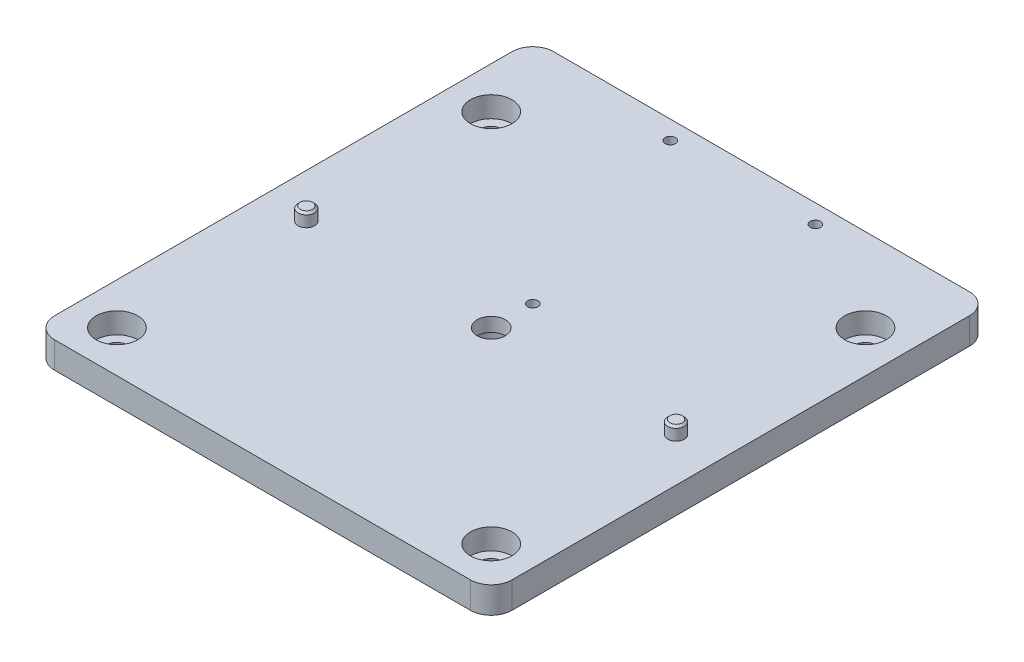
SolidWorks part; units mm, degrees
material "6061 Alloy"
ref_plane "Front Plane" through (0, 0, 0) normal (0, 0, 1) x (1, 0, 0)
ref_plane "Top Plane" through (0, 0, 0) normal (0, 1, 0) x (1, 0, 0)
ref_plane "Right Plane" through (0, 0, 0) normal (1, 0, 0) x (0, 0, -1)
sketch "Sketch1" plane through (0, 0, 0) normal (0, 1, 0) x (1, 0, 0)
  line L1 (-50, -55) -> (50, -55)
  line L2 (-55, -50) -> (-55, 55)
  line L3 (-55, 55) -> (55, 55)
  line L4 (55, -50) -> (55, 55)
  line L5 (-55, -55) -> (55, 55) construction
  line L6 (-55, 55) -> (55, -55) construction
  arc A0 (-55, -50) -> (-50, -55) centre (-50, -50) ccw
  arc A1 (50, -55) -> (55, -50) centre (50, -50) ccw
  point P0 (0, 0)
  dimension "D3" = 5
  dimension "D1" = 110
  dimension "D2" = 110
extrude "Boss-Extrude1" add sketch "Sketch1" along normal blind 6.35
sketch "Sketch9" plane through (0, 0, 0) normal (0, 1, 0) x (1, 0, 0)
  line L0 (55, 55) -> (20, 65)
  line L1 (55, 55) -> (-55, 55) construction
  line L2 (20, 65) -> (-20, 65)
  line L3 (-20, 65) -> (-55, 55)
  line L4 (55, 55) -> (-55, 55) construction
  line L5 (55, 55) -> (-55, 55)
  point P11 (0, 65)
  dimension "D1" = 10
  dimension "D2" = 40
hole_wizard "CBORE for 1/4 Socket Head Cap Screw1" positions "Sketch2" profile "Sketch4" counterbore size "1/4" standard "ANSI Inch" end condition through all
sketch "Sketch2" plane through (0, 0, 0) normal (0, -1, 0) x (-1, 0, 0)
  point P0 (0, 0)
sketch "Sketch4" plane through (0, 0, 0) normal (1, 0, 0) x (0, 0, -1)
  line L0 (0, 0) -> (0, 6.35)
  line L1 (0, 6.35) -> (3.3782, 6.35)
  line L3 (3.3782, 6.35) -> (3.3782, 3)
  line L4 (3.3782, 3) -> (5.5562, 3)
  line L5 (5.5562, 3) -> (5.5562, 0)
  line L7 (5.5562, 0) -> (0, 0)
  line L11 (0, -6.35) -> (0, 107.95) construction
  dimension "Thru Hole Dia." = 6.7564
  dimension "Thru Hole Depth" = 6.35
  dimension "C'Bore Dia." = 11.1125
  dimension "C'Bore Depth" = 3
hole_wizard "CBORE for M5 SHCS1" positions "Sketch5" profile "Sketch6" counterbore size "M5" standard "ANSI Metric"
sketch "Sketch5" plane through (0, 6.35, 0) normal (0, 1, 0) x (1, 0, 0)
  line L1 (55, 55) -> (-55, 55) construction
  line L2 (0, 0) -> (52.5, 0) construction
  line L4 (0, 0) -> (0, 55) construction
  point P0 (45, 45)
  point P16 (45, -45)
  point P17 (-45, -45)
  point P18 (-45, 45)
  dimension "D1" = 45
  dimension "D2" = 45
sketch "Sketch6" plane through (45, 6.35, -45) normal (1, 0, 0) x (0, 0, 1)
  line L0 (0, 0) -> (0, 13.2424)
  line L1 (0, 13.2424) -> (2.75, 11.59)
  line L2 (2.75, 11.59) -> (2.75, 5)
  line L3 (2.75, 5) -> (5, 5)
  line L4 (5, 5) -> (5, 0)
  line L5 (5, 0) -> (0, 0)
  line L10 (0, 13.2424) -> (-2.75, 11.59) construction
  line L11 (0, -6.35) -> (0, 107.95) construction
  dimension "Hole Dia." = 5.5
  dimension "Hole Depth" = 11.59
  dimension "C'Bore Dia." = 10
  dimension "C'Bore Depth" = 5
  dimension "Drill Angle" = 118
hole_wizard "1/8 (0.125) Press Dowel Hole1" positions "Sketch7" profile "Sketch8" hole size "1/8" standard "ANSI Inch" end condition through all
sketch "Sketch7" plane through (0, 6.35, 0) normal (0, 1, 0) x (1, 0, 0)
  line L0 (0, 0) -> (0, -55) construction
  line L1 (-50, -55) -> (50, -55) construction
  point P0 (-44.45, 0)
  point P2 (44.45, 0)
  dimension "D1" = 88.9
sketch "Sketch8" plane through (-44.45, 6.35, 0) normal (1, 0, 0) x (0, 0, 1)
  line L0 (0, 0) -> (0, 6.35)
  line L1 (0, 6.35) -> (1.9844, 6.35)
  line L2 (1.9844, 6.35) -> (1.9844, 0)
  line L5 (1.9844, 0) -> (0, 0)
  line L11 (0, -6.35) -> (0, 107.95) construction
  dimension "Thru Hole Dia." = 3.9688
  dimension "Thru Hole Depth" = 6.35
extrude "Boss-Extrude2" [suppressed] add sketch "Sketch9" along normal blind 6.35 contours L2 L3 L5 L0
sketch "Sketch12" plane through (0, 0, -55) normal (0, 0, -1) x (-1, 0, 0)
  line L0 (55, 6.35) -> (55, 0) construction
  line L1 (-55, 6.35) -> (-55, 0) construction
  line L2 (-55, 0) -> (55, 0) construction
  line L3 (-55, 6.35) -> (55, 6.35) construction
  line L4 (55, 6.35) -> (55, 0)
  line L5 (-55, 6.35) -> (-55, 0)
  line L6 (-55, 0) -> (55, 0)
  line L7 (-55, 6.35) -> (55, 6.35)
extrude "Boss-Extrude3" add sketch "Sketch12" along normal blind 10
fillet "Fillet1" radius 5 2 edges at (-55, 3.175, -65) (55, 3.175, -65)
hole_wizard "M3x0.5 Tapped Hole1" positions "Sketch10" profile "Sketch11" tap size "M3x0.5" standard "ANSI Metric" end condition through all
sketch "Sketch10" plane through (0, 0, 0) normal (0, -1, 0) x (-1, 0, 0)
  point P1 (-17.45, 60.5)
  point P4 (17.45, 60.5)
  point P7 (0, 10)
  dimension "D1" = 50.5
  dimension "D2" = 34.9
  dimension "D3" = 10
  dimension "D4" = 17.45
sketch "Sketch11" plane through (17.45, 0, -60.5) normal (1, 0, 0) x (0, 0, -1)
  line L0 (0, 0) -> (0, 6.35)
  line L1 (0, 6.35) -> (1.25, 6.35)
  line L2 (1.25, 6.35) -> (1.25, 0)
  line L5 (1.25, 0) -> (0, 0)
  line L11 (0, -6.35) -> (0, 107.95) construction
  dimension "Thru Tap Drill Dia." = 2.5
  dimension "Thru Tap Drill Depth" = 6.35
cosmetic thread "Hole Thread1" parameters "D2"=3
cosmetic thread "Hole Thread2" parameters "D2"=3
cosmetic thread "Hole Thread3" parameters "D2"=3
sketch "Sketch13" plane through (0, 0, 0) normal (0, 1, 0) x (1, 0, 0)
  circle A0 centre (44.45, 0) radius 1.9844
  circle A1 centre (-44.45, 0) radius 1.9844
  dimension "D1" = 3.9688
extrude "Boss-Extrude4" add sketch "Sketch13" along normal blind 9.525 separate body
chamfer "Chamfer1" distance 0.5 angle 45 2 edges at (44.45, 0, 1.9844) (44.45, 9.525, 1.9844)
chamfer "Chamfer2" distance 0.5 angle 45 2 edges at (-44.45, 0, 1.9844) (-44.45, 9.525, 1.9844)
